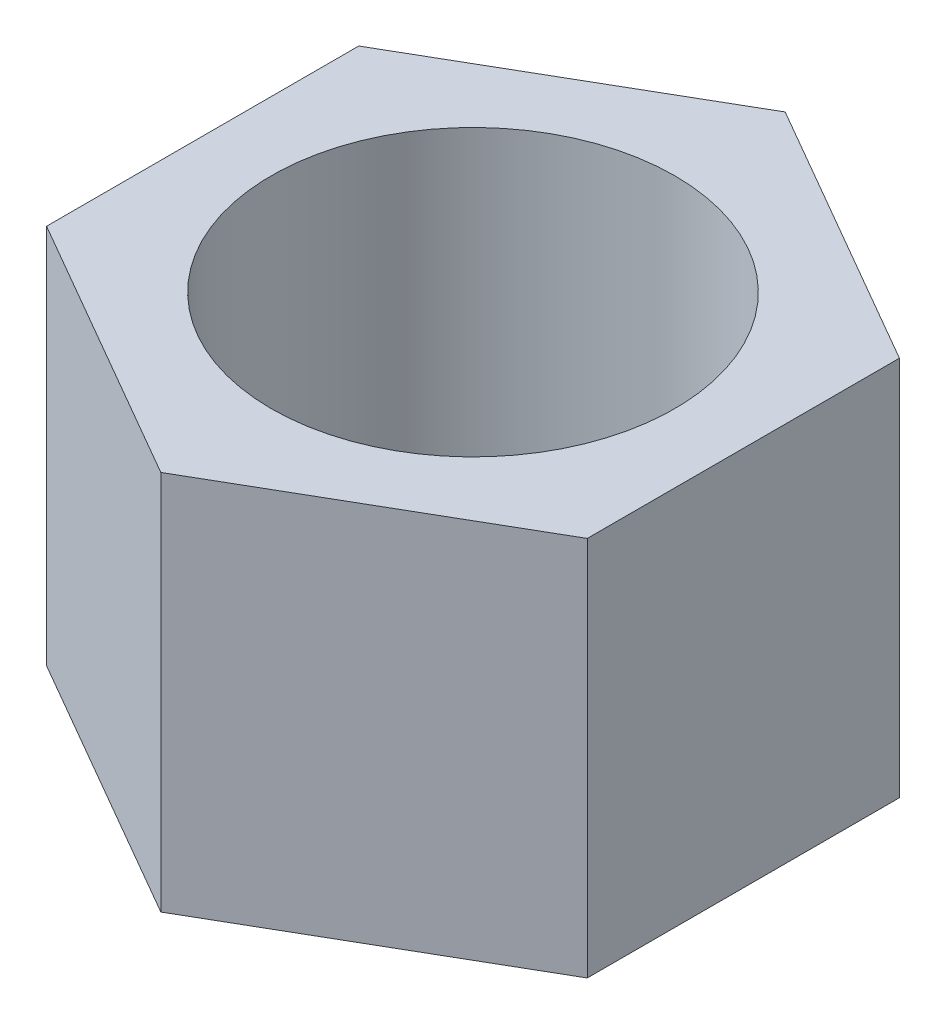
SolidWorks part; units mm, degrees
ref_plane "Front Plane" through (0, 0, 0) normal (0, 0, 1) x (1, 0, 0)
ref_plane "Top Plane" through (0, 0, 0) normal (0, 1, 0) x (1, 0, 0)
ref_plane "Right Plane" through (0, 0, 0) normal (1, 0, 0) x (0, 0, -1)
sketch "Sketch2" plane through (0, 0, 0) normal (0, 1, 0) x (1, 0, 0)
  line L0 (-3.5507, 2.05) -> (0, 4.1)
  line L1 (0, 4.1) -> (3.5507, 2.05)
  line L2 (3.5507, 2.05) -> (3.5507, -2.05)
  line L3 (3.5507, -2.05) -> (0, -4.1)
  line L4 (0, -4.1) -> (-3.5507, -2.05)
  line L5 (-3.5507, -2.05) -> (-3.5507, 2.05)
  circle A0 centre (0, 0) radius 4.1 construction
  circle A1 centre (0, 0) radius 2.65
  point P2 (0, 4.1)
  point P5 (3.5507, 2.05)
  point P6 (3.5507, -2.05)
  point P7 (0, -4.1)
  point P10 (-3.5507, -2.05)
  point P11 (-3.5507, 2.05)
  point P12 (0, 0)
  dimension "D1" = 8.2
  dimension "D3" = 5.3
  dimension "D2" = 6
extrude "Boss-Extrude1" add sketch "Sketch2" along normal blind 5
